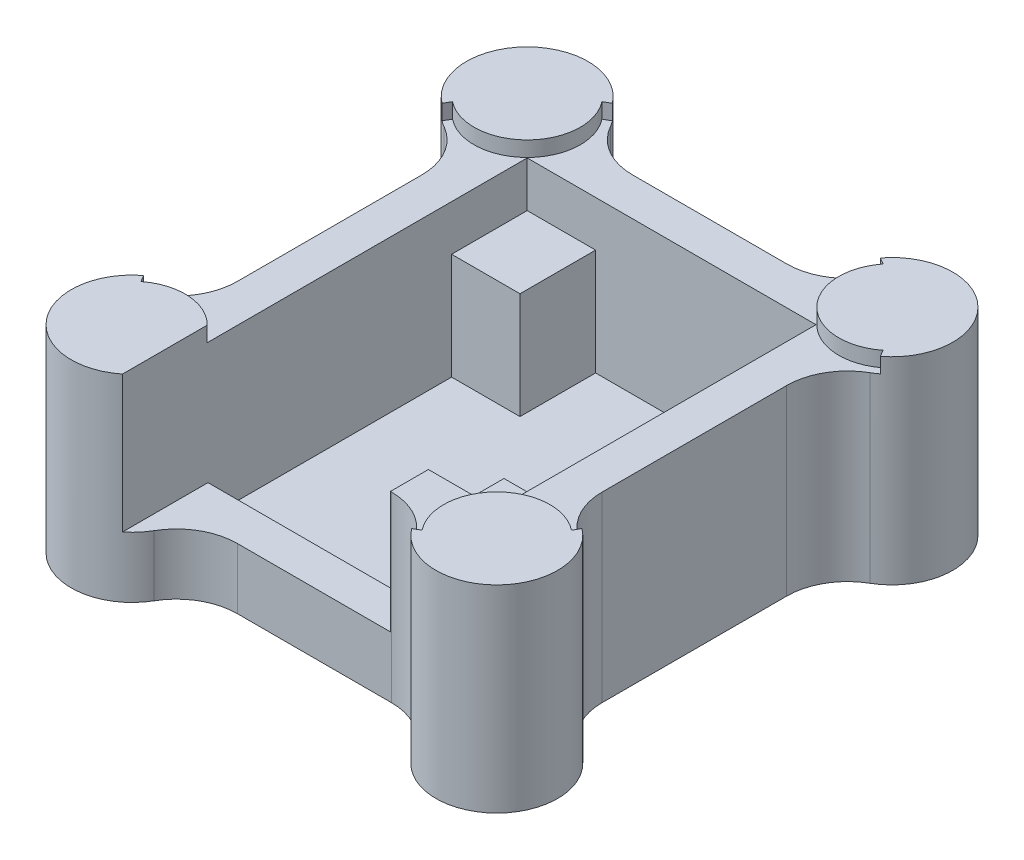
SolidWorks part; units mm, degrees
ref_plane "Front Plane" through (0, 0, 0) normal (0, 0, 1) x (1, 0, 0)
ref_plane "Top Plane" through (0, 0, 0) normal (0, 1, 0) x (1, 0, 0)
ref_plane "Right Plane" through (0, 0, 0) normal (1, 0, 0) x (0, 0, -1)
sketch "Sketch1" plane through (0, 0, 0) normal (0, 1, 0) x (1, 0, 0)
  line L0 (-12, 13) -> (-12, 9) construction
  line L1 (-8, -13) -> (8, -13)
  line L2 (-12, -9) -> (-12, 9)
  line L3 (-8, 13) -> (8, 13)
  line L4 (12, -9) -> (12, 9)
  line L5 (-12, -13) -> (12, 13) construction
  line L6 (-12, 13) -> (12, -13) construction
  line L7 (8, -13) -> (-8, -13) construction
  line L8 (12, -9) -> (12, 9) construction
  line L9 (8, 13) -> (-8, 13) construction
  line L10 (-12, -9) -> (-12, 9) construction
  line L11 (12, -13) -> (-12, 13) construction
  line L12 (12, 13) -> (-12, -13) construction
  line L13 (-12, 13) -> (-8, 13) construction
  line L14 (8, 13) -> (12, 13) construction
  line L15 (12, 13) -> (12, 9) construction
  line L16 (12, -9) -> (12, -13) construction
  line L17 (8, -13) -> (12, -13) construction
  line L18 (-8, -13) -> (-12, -13) construction
  line L19 (-12, -9) -> (-12, -13) construction
  arc A0 (-8, 13) -> (-12, 9) centre (-12, 13) ccw
  arc A1 (12, 9) -> (8, 13) centre (12, 13) ccw
  arc A2 (8, -13) -> (12, -9) centre (12, -13) ccw
  arc A3 (-12, -9) -> (-8, -13) centre (-12, -13) ccw
  point P0 (0, 0)
  point P8 (0, 0)
  dimension "D3" = 8
  dimension "D1" = 24
  dimension "D2" = 26
extrude "Boss-Extrude1" add sketch "Sketch1" along normal blind 12
sketch "Sketch2" plane through (0, 12, 0) normal (0, 1, 0) x (1, 0, 0)
  line L0 (-9.5, 5.5263) -> (-9.5, 10.5) construction
  line L1 (-9.5, -10.5) -> (5, -10.5)
  line L2 (-9.5, -10.5) -> (-9.5, 5.5263)
  line L3 (-5, 10.5) -> (9.5, 10.5)
  line L4 (9.5, -5.5263) -> (9.5, 10.5)
  line L5 (-9.5, -10.5) -> (9.5, 10.5) construction
  line L6 (-9.5, 10.5) -> (9.5, -10.5) construction
  line L9 (9.5, -5.5263) -> (5, -5.5263)
  line L10 (5, -10.5) -> (5, -5.5263)
  line L13 (-9.5, 5.5263) -> (-5, 5.5263)
  line L14 (-5, 10.5) -> (-5, 5.5263)
  line L15 (-5, 10.5) -> (-9.5, 10.5) construction
  line L16 (9.5, -10.5) -> (9.5, -5.5263) construction
  line L17 (9.5, -10.5) -> (5, -10.5) construction
  point P0 (0, 0)
  dimension "D1" = 19
  dimension "D2" = 21
  dimension "D3" = 5
extrude "Cut-Extrude1" cut sketch "Sketch2" against normal offset from surface (10 mm away) 2 up to face at (0, 0, 0)
sketch "Sketch5" plane through (0, 12, 0) normal (0, 1, 0) x (1, 0, 0)
  circle A0 centre (-12, 13) radius 0.75
  circle A1 centre (12, 13) radius 0.75
  circle A2 centre (12, -13) radius 0.75
  circle A3 centre (-12, -13) radius 0.75
  dimension "D1" = 1.5
extrude "Cut-Extrude4" [suppressed] cut sketch "Sketch5" against normal blind 7
sketch "Sketch6" [suppressed] plane through (0, 0, 0) normal (0, -1, 0) x (1, 0, 0)
  line L1 (-9.5, 16.1225) -> (5, 16.1225)
  line L2 (-9.5, 16.1225) -> (-9.5, 5.5263)
  line L3 (-9.5, 5.5263) -> (5, 5.5263)
  line L4 (5, 16.1225) -> (5, 5.5263)
  line L5 (-9.5, -5.5263) -> (-9.5, 10.5) construction
  arc A0 (-8, 13) -> (-12, 9) centre (-12, 13) ccw construction
extrude "Cut-Extrude5" [suppressed] cut sketch "Sketch6" against normal offset from surface (3 mm away) 1
sketch "Sketch7" [suppressed] plane through (0, 4, 0) normal (0, 1, 0) x (1, 0, 0)
  circle A0 centre (-12, 13) radius 1.5
  circle A1 centre (12, 13) radius 1.5
  circle A2 centre (12, -13) radius 1.5
  circle A3 centre (-12, -13) radius 1.5
  dimension "D1" = 3
extrude "Cut-Extrude6" [suppressed] cut sketch "Sketch7" against normal through all
chamfer "Chamfer1" [suppressed] distance 1 angle 45
fillet "Fillet1" radius 4 8 edges at (-8, 6, 13) (8, 6, 13) (12, 6, 9) (12, 6, -9) (8, 6, -13) (-8, 6, -13) (-12, 6, 9) (-12, 6, -9)
sketch "Sketch8" [suppressed] plane through (0, 0, 0) normal (0, -1, 0) x (1, 0, 0)
  line L1 (5, 5.5263) -> (9, 5.5263)
  line L2 (5, 5.5263) -> (5, 9.5263)
  line L3 (5, 9.5263) -> (9, 9.5263)
  line L4 (9, 5.5263) -> (9, 9.5263)
  line L5 (-5, -5.5263) -> (-9, -5.5263)
  line L6 (-5, -5.5263) -> (-5, -9.5263)
  line L7 (-5, -9.5263) -> (-9, -9.5263)
  line L8 (-9, -5.5263) -> (-9, -9.5263)
  dimension "D1" = 4
extrude "Boss-Extrude2" [suppressed] add sketch "Sketch8" along normal blind 1
sketch "Sketch9" [suppressed] plane through (0, 0, 0) normal (0, -1, 0) x (1, 0, 0)
  circle A0 centre (-12, 13) radius 4
  circle A1 centre (12, 13) radius 4
  circle A2 centre (12, -13) radius 4
  circle A3 centre (-12, -13) radius 4
  arc A4 (-14, -9.5359) -> (-8.5359, -15) centre (-12, -13) ccw construction
  arc A5 (8.5359, -15) -> (14, -9.5359) centre (12, -13) ccw construction
  arc A6 (14, 9.5359) -> (8.5359, 15) centre (12, 13) ccw construction
  arc A7 (-9.5, 16.1225) -> (-14, 9.5359) centre (-12, 13) ccw construction
extrude "Cut-Extrude7" [suppressed] cut sketch "Sketch9" against normal blind 1
sketch "Sketch10" plane through (0, 12, 0) normal (0, 1, 0) x (1, 0, 0)
  line L2 (12, -13) -> (8.5359, -15) construction
  line L3 (12, -13) -> (14, -9.5359) construction
  line L6 (14.4173, -9.8131) -> (14.1651, -10.25)
  line L7 (8.8131, -15.4173) -> (9.25, -15.1651)
  line L8 (14.2912, -10.0315) -> (13.8582, -9.7815) construction
  line L9 (9.0315, -15.2912) -> (8.7815, -14.8582) construction
  arc A2 (8.8131, -15.4173) -> (14.4173, -9.8131) centre (12, -13) ccw
  arc A5 (8.5359, -15) -> (14, -9.5359) centre (12, -13) ccw construction
  arc A11 (14.1651, -10.25) -> (9.25, -15.1651) centre (12, -13) ccw
  dimension "D2" = 0.5
  dimension "D3" = 0.5
extrude "Boss-Extrude3" add sketch "Sketch10" along normal blind 1
mirror "Mirror1" about plane through (0, 0, 0) normal (1, 0, 0) of "Boss-Extrude3"
mirror "Mirror2" about plane through (0, 0, 0) normal (0, 0, 1) of "Mirror1", "Boss-Extrude3"
sketch "Sketch3" plane through (0, 12, 0) normal (0, 1, 0) x (1, 0, 0)
  line L0 (-9.5, 5.5263) -> (-9.5, -10.5) construction
  line L1 (5, -10.5) -> (-9.5, -10.5)
  line L2 (5, -10.5) -> (5, -16.1225)
  line L3 (5, -16.1225) -> (-9.5, -16.1225)
  line L4 (-9.5, -10.5) -> (-9.5, -16.1225)
  arc A0 (-16, -13) -> (-12, -17) centre (-12, -13) ccw construction
extrude "Cut-Extrude2" cut sketch "Sketch3" against normal offset from surface 2 and the other way through all up to face at (0, 2, 0)
sketch "Sketch4" plane through (0, 12, 0) normal (0, 1, 0) x (1, 0, 0)
  line L0 (-5, 10.5) -> (-9.5, 10.5)
  line L1 (-9.5, 10.5) -> (-9.5, 5.5263)
  line L2 (-9.5, 5.5263) -> (-5, 5.5263)
  line L3 (-5, 10.5) -> (-5, 5.5263)
  line L4 (5, -5.5263) -> (5, -10.5)
  line L5 (5, -10.5) -> (9.5, -10.5)
  line L6 (9.5, -10.5) -> (9.5, -5.5263)
  line L7 (9.5, -5.5263) -> (5, -5.5263)
extrude "Cut-Extrude3" cut sketch "Sketch4" against normal blind 3
